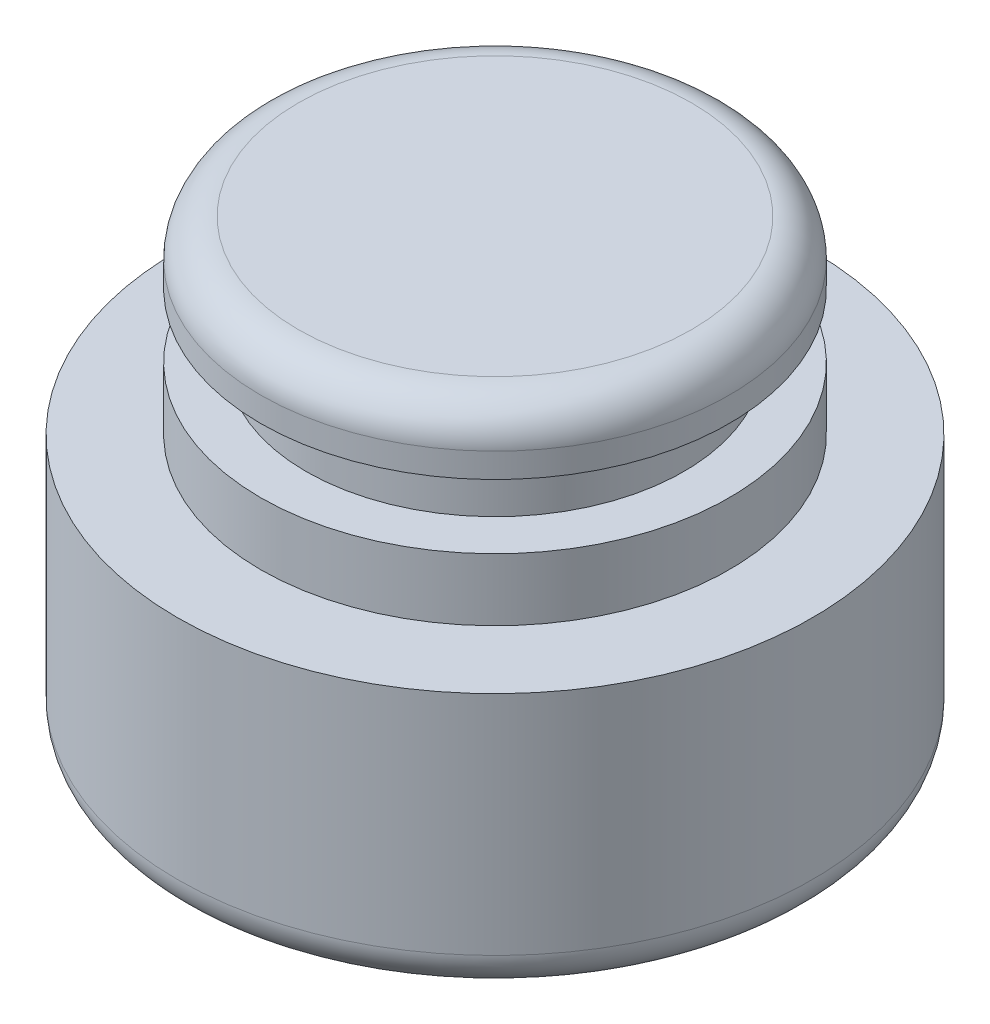
SolidWorks part; units mm, degrees
ref_plane "Front" through (0, 0, 0) normal (0, 0, 1) x (1, 0, 0)
ref_plane "Top" through (0, 0, 0) normal (0, 1, 0) x (1, 0, 0)
ref_plane "Right" through (0, 0, 0) normal (1, 0, 0) x (0, 0, -1)
sketch "Sketch1" plane through (0, 0, 0) normal (0, 0, 1) x (1, 0, 0)
  line L0 (0, 0) -> (0, 12)
  line L1 (0, 0) -> (8.4, 0)
  line L2 (8.4, 0) -> (8.4, 7)
  line L3 (0, 12) -> (6.2, 12)
  line L4 (6.2, 12) -> (6.2, 10.35)
  line L5 (6.2, 10.35) -> (5, 10.35)
  line L6 (5, 10.35) -> (5, 8.65)
  line L7 (5, 8.65) -> (6.2, 8.65)
  line L8 (6.2, 8.65) -> (6.2, 7)
  line L9 (6.2, 7) -> (8.4, 7)
revolve "Revolve1" add sketch "Sketch1" angle 360 about L0
fillet "Fillet1" radius 1 1 edges at (0, 12, -6.2)
fillet "Fillet2" radius 1 1 edges at (0, 0, -8.4)
